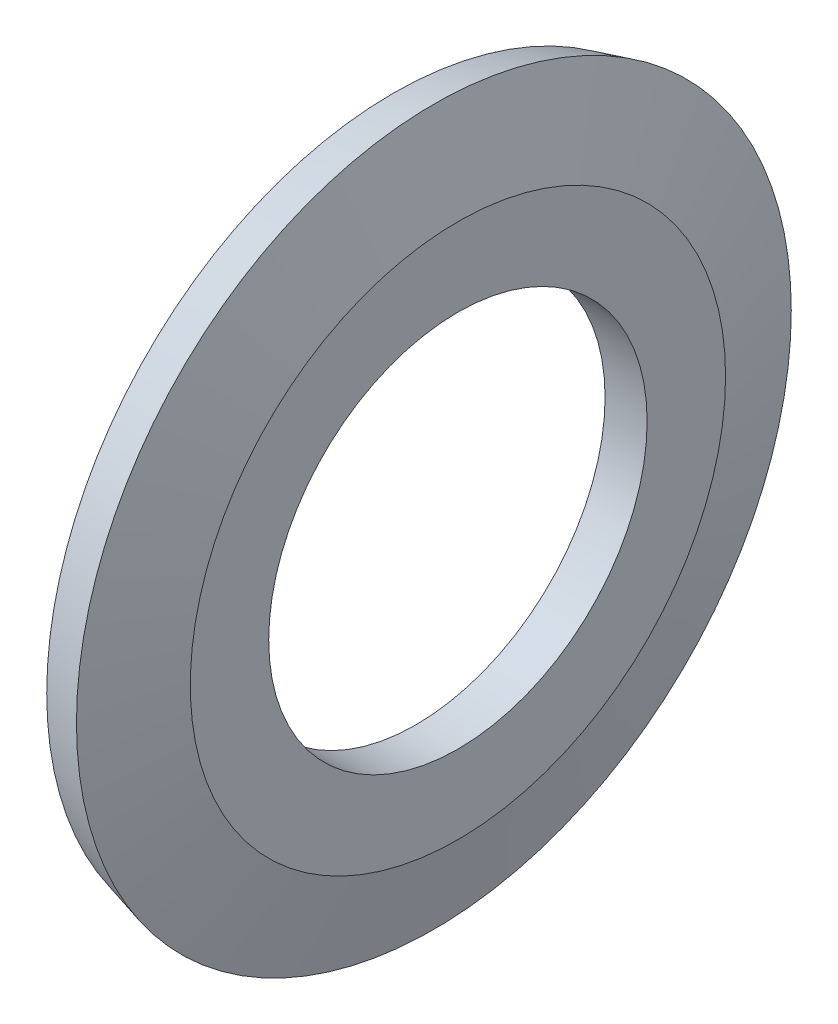
SolidWorks part; units mm, degrees
ref_plane "Front Plane" through (0, 0, 0) normal (0, 0, 1) x (1, 0, 0)
ref_plane "Top Plane" through (0, 0, 0) normal (0, 1, 0) x (1, 0, 0)
ref_plane "Right Plane" through (0, 0, 0) normal (1, 0, 0) x (0, 0, -1)
sketch "Sketch1" plane through (0, 0, 0) normal (0, 0, 1) x (1, 0, 0)
  line L0 (1, 4.5) -> (0, 4.5)
  line L1 (0, 4.5) -> (0, 6.2333)
  line L2 (1, 4.5) -> (1, 6.365)
  line L3 (1, 6.365) -> (0.4279, 8.5)
  line L4 (0.4279, 8.5) -> (-0.538, 8.2412)
  line L5 (-0.538, 8.2412) -> (0, 6.2333)
  line L6 (1, 0) -> (0, 0) construction
  dimension "D1" = 1
  dimension "D2" = 15
  dimension "E" = 9
  dimension "P.D." = 12.73
  dimension "F_1" = 17
revolve "Revolve1" add sketch "Sketch1" angle 360 about L6
sketch "Sketch2" [suppressed] plane through (0, 0, 0) normal (0, 0, 1) x (1, 0, 0)
  line L0 (-0.475, 0) -> (0, 0) construction
  line L1 (-0.475, 21) -> (1, 21)
  line L2 (-0.475, 21) -> (-0.475, 20)
  line L3 (-0.475, 20) -> (1, 20)
  line L4 (1, 21) -> (1, 20)
  line L7 (1, -19.1) -> (1, 19.1) construction
  line L8 (-0.475, 20.7412) -> (-0.475, -20.7412) construction
  dimension "FC" = 40
revolve "Cut-Revolve1" [suppressed] cut sketch "Sketch2" angle 360 about L0
